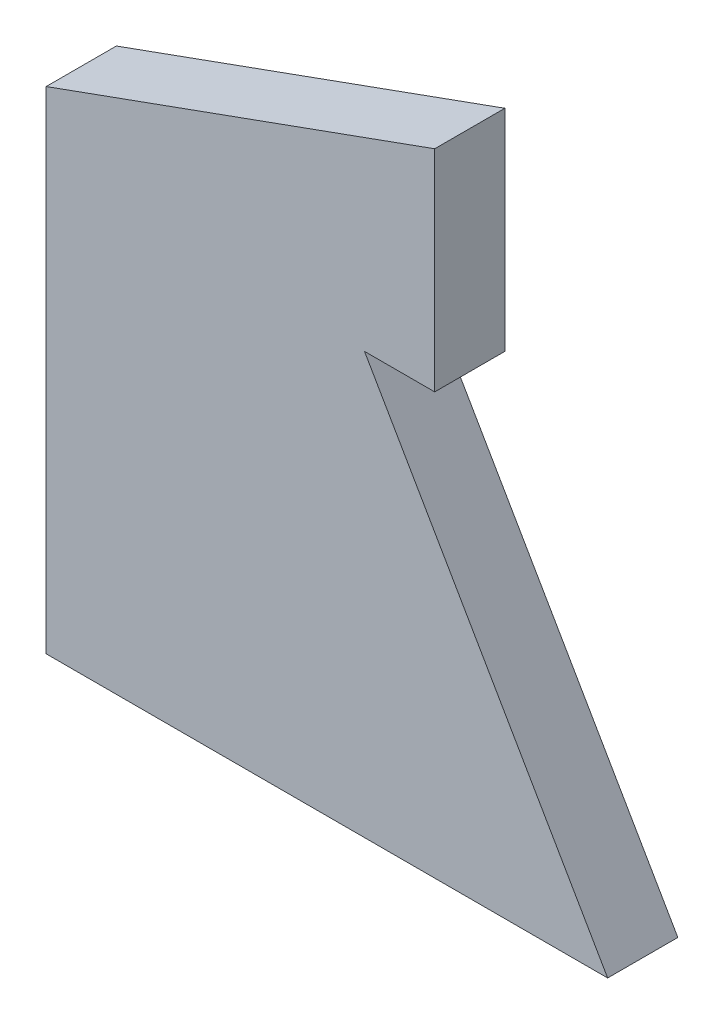
SolidWorks part; units mm, degrees
ref_plane "Přední rovina" through (0, 0, 0) normal (0, 0, 1) x (1, 0, 0)
ref_plane "Vrchní rovina" through (0, 0, 0) normal (0, 1, 0) x (1, 0, 0)
ref_plane "Pravá rovina" through (0, 0, 0) normal (1, 0, 0) x (0, 0, -1)
sketch "Skica1" plane through (0, 0, 0) normal (0, 0, 1) x (1, 0, 0)
  line L0 (0, 0) -> (80, 0)
  line L1 (80, 0) -> (45.359, 60)
  line L2 (45.359, 60) -> (55.359, 60)
  line L3 (55.359, 60) -> (55.359, 90)
  line L4 (55.359, 90) -> (0, 70)
  line L5 (0, 70) -> (0, 0)
  point P3 (62.0834, 47.4529)
  point P8 (85.7617, 55.3457)
  point P9 (0, 0)
  point P10 (0, 0)
  dimension "D1" = 80
  dimension "D2" = 70
  dimension "D3" = 60
  dimension "D4" = 90
  dimension "D5" = 10
  dimension "D6" = 60
extrude "Přidat vysunutím1" add sketch "Skica1" along normal blind 10
